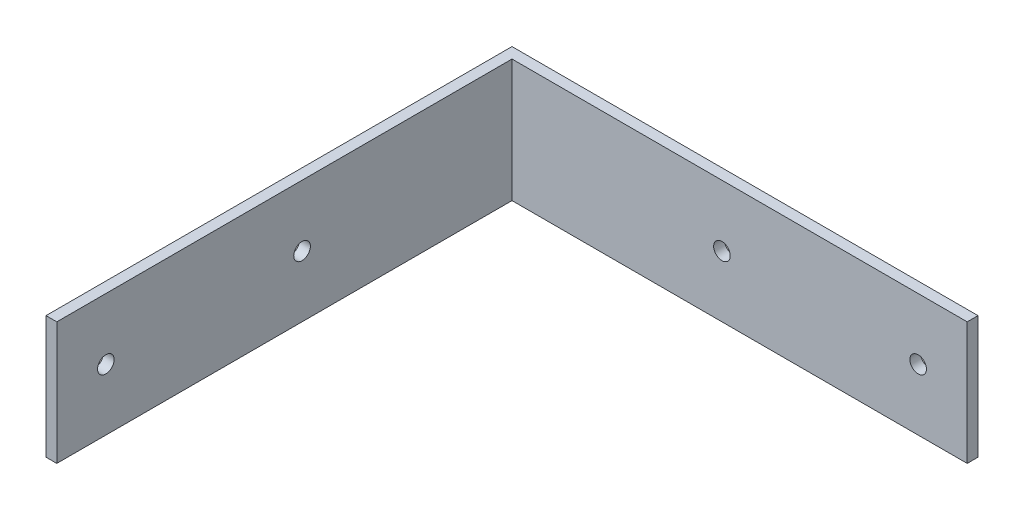
SolidWorks part; units mm, degrees
material "Plain Carbon Steel"
ref_plane "Front Plane" through (0, 0, 0) normal (0, 0, 1) x (1, 0, 0)
ref_plane "Top Plane" through (0, 0, 0) normal (0, 1, 0) x (1, 0, 0)
ref_plane "Right Plane" through (0, 0, 0) normal (1, 0, 0) x (0, 0, -1)
sketch "Sketch1" plane through (0, 0, 0) normal (0, 1, 0) x (1, 0, 0)
  line L1 (0, 0) -> (120.65, 0)
  line L3 (2.794, -2.794) -> (120.65, -2.794)
  line L4 (120.65, 0) -> (120.65, -2.794)
  line L6 (0, 0) -> (0, -120.65)
  line L7 (0, -120.65) -> (2.794, -120.65)
  line L8 (2.794, -2.794) -> (2.794, -120.65)
  dimension "D1" = 120.65
  dimension "D2" = 120.65
  dimension "D3" = 2.794
extrude "Boss-Extrude1" add sketch "Sketch1" along normal blind 31.75
hole_wizard "#8 Clearance Hole1" positions "Sketch3" profile "Sketch4" hole size "#8" standard "ANSI Inch"
sketch "Sketch3" plane through (0, 0, 0) normal (0, 0, -1) x (-1, 0, 0)
  line L0 (-120.65, 15.875) -> (-107.95, 15.875) construction
  line L1 (-120.65, 31.75) -> (-120.65, 0) construction
  line L2 (-107.95, 15.875) -> (-57.15, 15.875) construction
  line L3 (-57.15, 15.875) -> (-44.45, 15.875) construction
  point P1 (-107.95, 15.875)
  point P5 (-57.15, 15.875)
  dimension "D1" = 76.2
  dimension "D2" = 12.7
sketch "Sketch4" plane through (107.95, 15.875, 0) normal (1, 0, 0) x (0, 1, 0)
  line L0 (0, 0) -> (0, 7.6434)
  line L1 (0, 7.6434) -> (2.1526, 6.35)
  line L2 (2.1526, 6.35) -> (2.1526, 0)
  line L5 (2.1526, 0) -> (0, 0)
  line L10 (0, 7.6434) -> (-2.1527, 6.35) construction
  line L11 (0, -6.35) -> (0, 107.95) construction
  dimension "Hole Dia." = 4.3053
  dimension "Hole Depth" = 6.35
  dimension "Drill Angle" = 118
hole_wizard "#8 Clearance Hole2" positions "Sketch6" profile "Sketch5" hole size "#8" standard "ANSI Inch"
sketch "Sketch6" plane through (0, 0, 0) normal (-1, 0, 0) x (0, 0, 1)
  line L0 (120.65, 15.875) -> (107.95, 15.875) construction
  line L1 (120.65, 31.75) -> (120.65, 0) construction
  line L2 (107.95, 15.875) -> (57.15, 15.875) construction
  line L3 (57.15, 15.875) -> (44.45, 15.875) construction
  point P2 (107.95, 15.875)
  point P9 (57.15, 15.875)
  dimension "D1" = 12.7
  dimension "D2" = 76.2
sketch "Sketch5" plane through (0, 15.875, 107.95) normal (0, 1, 0) x (0, 0, 1)
  line L0 (0, 0) -> (0, 7.6434)
  line L1 (0, 7.6434) -> (2.1526, 6.35)
  line L2 (2.1526, 6.35) -> (2.1526, 0)
  line L5 (2.1526, 0) -> (0, 0)
  line L10 (0, 7.6434) -> (-2.1526, 6.35) construction
  line L11 (0, -6.35) -> (0, 107.95) construction
  dimension "Hole Dia." = 4.3053
  dimension "Hole Depth" = 6.35
  dimension "Drill Angle" = 118
